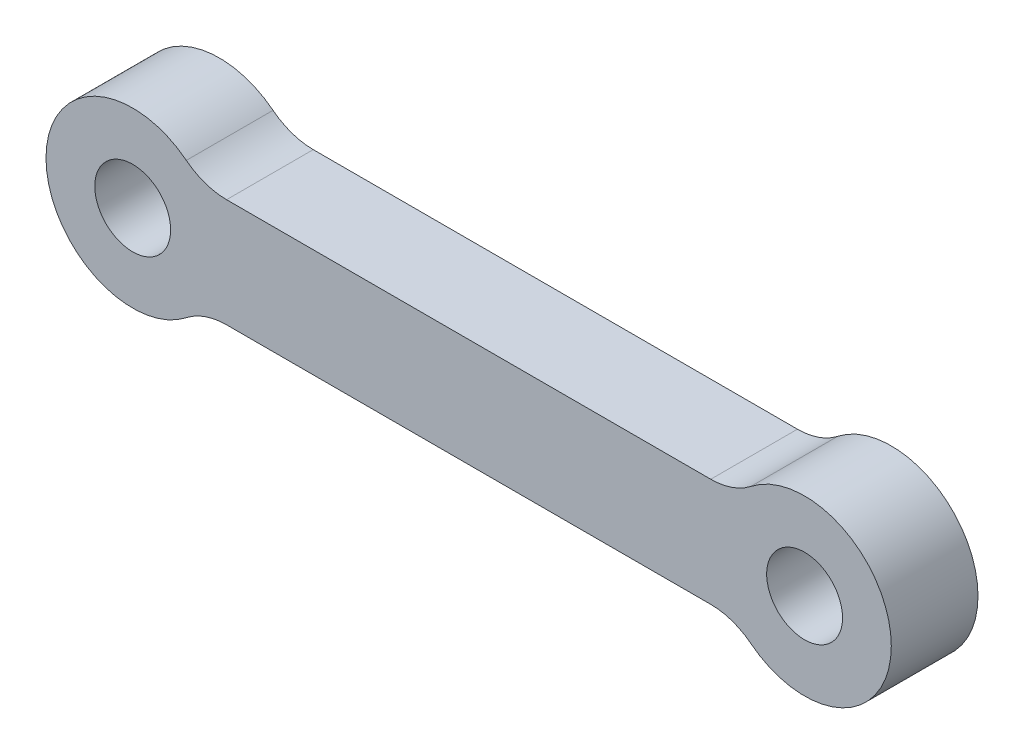
SolidWorks part; units mm, degrees
ref_plane "Front Plane" through (0, 0, 0) normal (0, 0, 1) x (1, 0, 0)
ref_plane "Top Plane" through (0, 0, 0) normal (0, 1, 0) x (1, 0, 0)
ref_plane "Right Plane" through (0, 0, 0) normal (1, 0, 0) x (0, 0, -1)
sketch "Sketch1" plane through (0, 0, 0) normal (0, 0, 1) x (1, 0, 0)
  line L0 (0, 0) -> (31, 0) construction
  line L1 (3.1225, 2.5) -> (27.8775, 2.5)
  line L2 (3.1225, -2.5) -> (27.8775, -2.5)
  circle A0 centre (0, 0) radius 4
  circle A1 centre (0, 0) radius 1.75
  circle A2 centre (31, 0) radius 1.75
  circle A3 centre (31, 0) radius 4
  dimension "D1" = 3.5
  dimension "D3" = 8
  dimension "D4" = 3.5
  dimension "D5" = 8
  dimension "D2" = 31
  dimension "D6" = 2.5
extrude "Boss-Extrude1" add sketch "Sketch1" along normal blind 4
fillet "Fillet1" radius 3 4 edges at (27.8775, -2.5, 2) (3.1225, -2.5, 2) (3.1225, 2.5, 2) (27.8775, 2.5, 2)
